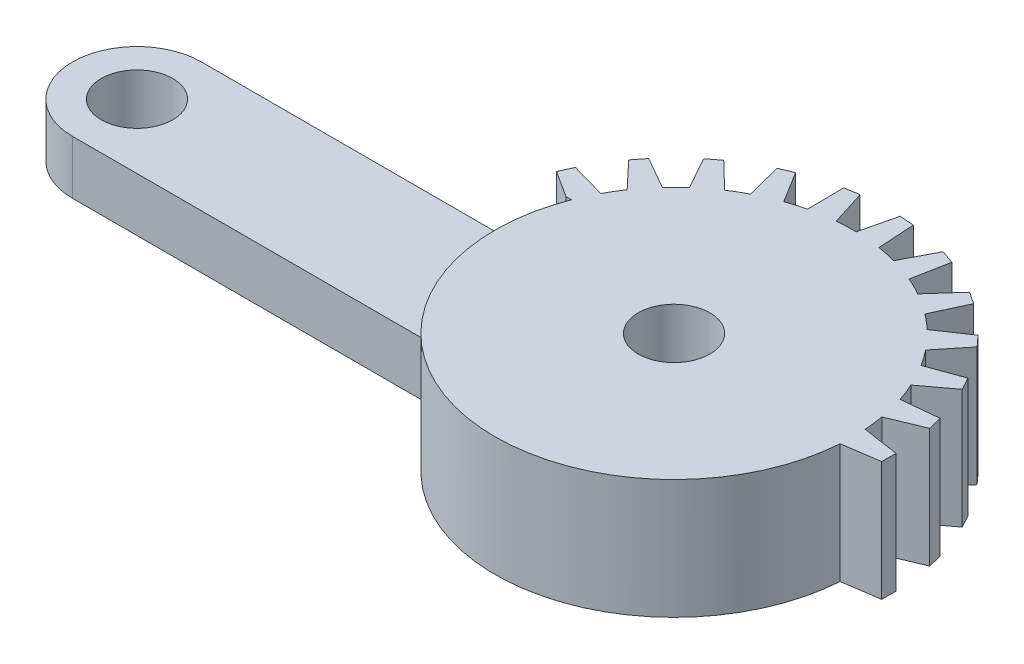
SolidWorks part; units mm, degrees
ref_plane "Front" through (0, 0, 0) normal (0, 0, 1) x (1, 0, 0)
ref_plane "Top" through (0, 0, 0) normal (0, 1, 0) x (1, 0, 0)
ref_plane "Right" through (0, 0, 0) normal (1, 0, 0) x (0, 0, -1)
sketch "Sketch1" plane through (0, 0, 0) normal (0, 1, 0) x (1, 0, 0)
  line L0 (-177.6425, 0) -> (70.7426, 0) construction
  line L1 (-150, 18) -> (-46.6476, 18)
  line L2 (-150, -18) -> (-46.6476, -18)
  arc A0 (-46.6476, -18) -> (-46.6476, 18) centre (0, 0) ccw
  arc A1 (-150, 18) -> (-150, -18) centre (-150, 0) ccw
  dimension "D1" = 100
  dimension "D3" = 150
  dimension "D2" = 18
extrude "Boss-Extrude1" add sketch "Sketch1" along normal blind 33.3333
sketch "Sketch2" plane through (0, 33.3333, 0) normal (0, 1, 0) x (1, 0, 0)
  line L0 (88.337, 0) -> (60, 0) construction
  line L1 (49.8773, 3.5) -> (60, 2)
  line L2 (60, 2) -> (60, -2)
  line L4 (50, 0) -> (49.8773, 3.5)
  line L5 (50, 0) -> (49.8773, -3.5)
  line L6 (49.8773, -3.5) -> (60, -2)
  line L7 (50, 0) -> (-74.3015, 0) construction
  line L8 (-46.6476, 18) -> (0, 0) construction
  arc A0 (-46.6476, -18) -> (-46.6476, 18) centre (0, 0) ccw construction
  arc A1 (49.8773, -3.5) -> (-46.6476, 18) centre (0, 0) ccw
  dimension "D1" = 4
  dimension "D2" = 10
  dimension "D3" = 3.5
extrude "Boss-Extrude2" add sketch "Sketch2" against normal up to surface (33.3333 mm away) contours L6 L2 L1 L4 L5 up to face at (-78.6619, 0, 0)
pattern_circular "CirPattern2" count 13 every 14.167 about axis through (0, 0, 0) along (0, 1, 0) of "Boss-Extrude2"
hole_wizard "Ø20.0mm 맞춤핀 구멍1" positions "Sketch4" profile "Sketch3" hole size "Ø20.0" standard "Ansi Metric" end condition through all
sketch "Sketch4" plane through (0, 33.3333, 0) normal (0, 1, 0) x (1, 0, 0)
  arc A0 (-150, 18) -> (-150, -18) centre (-150, 0) ccw construction
  point P0 (-150, 0)
  point P2 (0, 0)
  dimension "D1" = 0
sketch "Sketch3" plane through (-150, 33.3333, 0) normal (1, 0, 0) x (0, 0, 1)
  line L0 (0, 0) -> (0, 33.3333)
  line L1 (0, 33.3333) -> (10, 33.3333)
  line L2 (10, 33.3333) -> (10, 0)
  line L5 (10, 0) -> (0, 0)
  line L11 (0, -6.35) -> (0, 107.95) construction
  dimension "Thru Hole Dia." = 20
  dimension "Thru Hole Depth" = 33.3333
scale "축척1" scale about centroid uniform scaling yes scale factor 0.3
sketch "스케치1" plane through (0, 21.6667, 0) normal (0, 1, 0) x (1, 0, 0)
  line L0 (-36.6748, -4.0201) -> (-67.6805, -4.0201)
  line L2 (-37.1253, 6.7799) -> (-67.6805, 6.7799) construction
  line L3 (-67.6805, 6.7799) -> (-36.6748, 6.7799)
  arc A0 (-36.6748, 6.7799) -> (-36.6748, -4.0201) centre (-22.6805, 1.3799) ccw
  arc A1 (-67.6805, 6.7799) -> (-67.6805, -4.0201) centre (-67.6805, 1.3799) ccw construction
  arc A2 (-67.6805, 6.7799) -> (-67.6805, -4.0201) centre (-67.6805, 1.3799) ccw
extrude "컷-돌출1" cut sketch "스케치1" against normal blind 5.5
